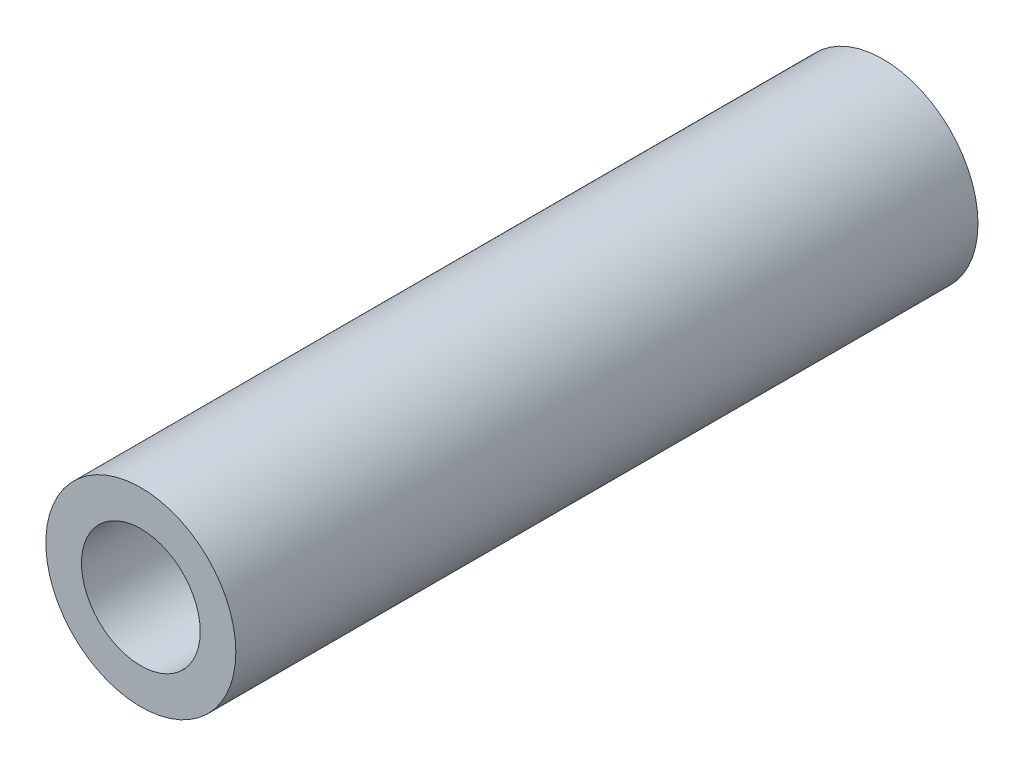
SolidWorks part; units mm, degrees
ref_plane "Front Plane" through (0, 0, 0) normal (0, 0, 1) x (1, 0, 0)
ref_plane "Top Plane" through (0, 0, 0) normal (0, 1, 0) x (1, 0, 0)
ref_plane "Right Plane" through (0, 0, 0) normal (1, 0, 0) x (0, 0, -1)
sketch "Sketch2" plane through (0, 0, 0) normal (0, 0, 1) x (1, 0, 0)
  line L0 (2, 22.6236) -> (2, -31.0228) construction
  line L1 (3.2, 22.6236) -> (3.2, -31.0228) construction
  circle A0 centre (0, 0) radius 3.2
  circle A1 centre (0, 0) radius 2 construction
  dimension "D1" = 1.2
  dimension "D2" = 4
extrude "Boss-Extrude1" add sketch "Sketch2" along normal blind 25 contours A0
sketch "Sketch3" plane through (0, 0, 25) normal (0, 0, 1) x (1, 0, 0)
  circle A0 centre (0, 0) radius 2
  point P2 (0, 0)
  dimension "D1" = 4
extrude "Cut-Extrude1" cut sketch "Sketch3" against normal blind 25
